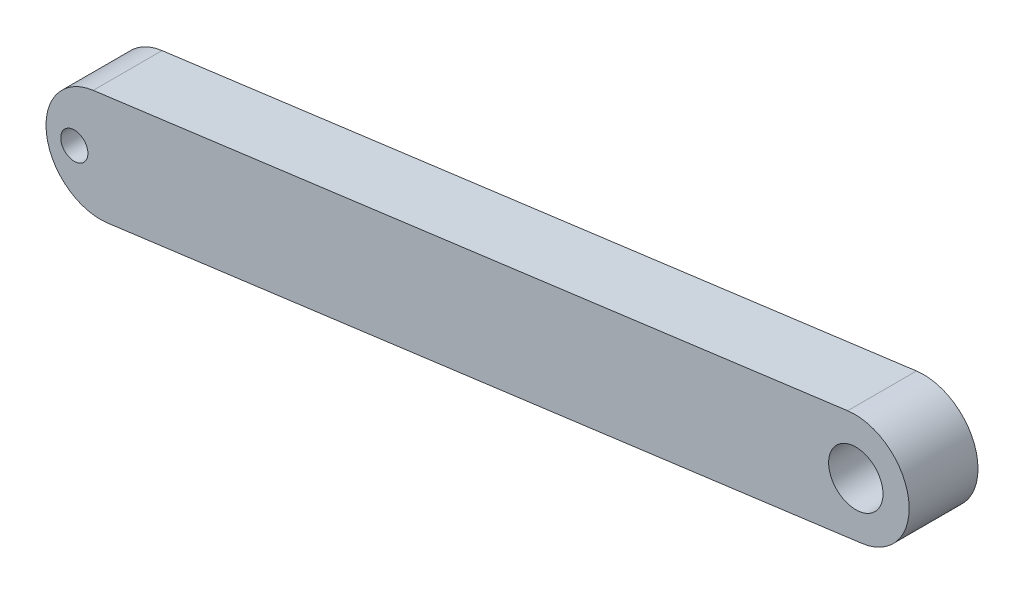
SolidWorks part; units mm, degrees
material "AISI 304"
ref_plane "Front Plane" through (0, 0, 0) normal (0, 0, 1) x (1, 0, 0)
ref_plane "Top Plane" through (0, 0, 0) normal (0, 1, 0) x (1, 0, 0)
ref_plane "Right Plane" through (0, 0, 0) normal (1, 0, 0) x (0, 0, -1)
sketch "Sketch1" plane through (0, 0, 0) normal (0, 0, 1) x (1, 0, 0)
  line L0 (4764.4519, -774.7161) -> (600.6861, -1325.2196)
  line L1 (4843.0953, -1369.5397) -> (679.3295, -1920.0433)
  arc A0 (4843.0953, -1369.5397) -> (4764.4519, -774.7161) centre (4803.7736, -1072.1279) ccw
  arc A2 (600.6861, -1325.2196) -> (679.3295, -1920.0433) centre (640.0078, -1622.6315) ccw
  point P3 (2761.2124, -1644.7915)
  dimension "D1" = 600
  dimension "D4" = 4200
  dimension "D5" = 4200
extrude "Boss-Extrude1" add sketch "Sketch1" along normal blind 380 contours L0 A2 L1 A0
sketch "Sketch2" plane through (0, 0, 380) normal (0, 0, 1) x (1, 0, 0)
  circle A0 centre (4809.3088, -1075.4757) radius 150
extrude "Cut-Extrude1" cut sketch "Sketch2" against normal through all
sketch "Sketch3" plane through (182.5208, -1380.5065, 0) normal (-0.1311, 0.9914, 0) x (0.9914, 0.1311, 0)
  line L0 (4621.8043, -380) -> (4621.8043, 0) construction
  line L1 (4621.8043, 0) -> (421.8043, 0) construction
  point P0 (4421.8043, -190)
  dimension "D1" = 200
  dimension "D2" = 190
ref_point "Point2"
sketch "Sketch4" plane through (0, 0, 380) normal (0, 0, 1) x (1, 0, 0)
  line L0 (4764.4519, -774.7161) -> (600.6861, -1325.2196) construction
  circle A0 centre (496.3088, -1641.6303) radius 75
  circle A4 centre (4809.3088, -1075.4757) radius 150 construction
  dimension "D1" = 150
  dimension "D2" = 300
  dimension "D3" = 4350
extrude "Cut-Extrude2" cut sketch "Sketch4" against normal through all contours A0
